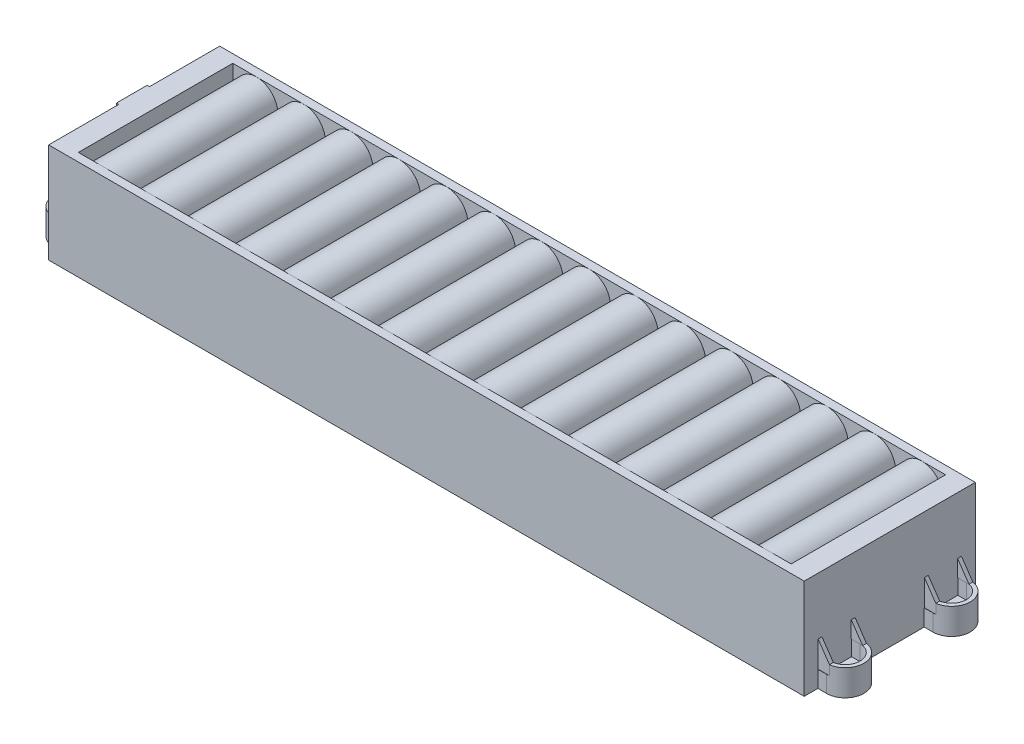
SolidWorks part; units mm, degrees
ref_plane "Front Plane" through (0, 0, 0) normal (0, 0, 1) x (1, 0, 0)
ref_plane "Top Plane" through (0, 0, 0) normal (0, 1, 0) x (1, 0, 0)
ref_plane "Right Plane" through (0, 0, 0) normal (1, 0, 0) x (0, 0, -1)
sketch "Sketch1" plane through (0, 0, 0) normal (0, 1, 0) x (1, 0, 0)
  line L1 (159, -36) -> (-159, -36)
  line L2 (159, -36) -> (159, 36)
  line L3 (159, 36) -> (-159, 36)
  line L4 (-159, -36) -> (-159, 36)
  line L5 (159, -36) -> (-159, 36) construction
  line L6 (159, 36) -> (-159, -36) construction
  point P0 (0, 0)
  dimension "D1" = 318
  dimension "D2" = 72
extrude "Boss-Extrude1" add sketch "Sketch1" along normal blind 42
sketch "Sketch2" plane through (0, 0, 0) normal (0, -1, 0) x (1, 0, 0)
  line L0 (162.625, 14.5) -> (159, 14.5)
  line L1 (159, 36) -> (159, -36) construction
  line L2 (162.625, 30.25) -> (159, 30.25)
  line L4 (162.625, 16.1) -> (159, 16.1)
  line L5 (162.625, 28.65) -> (159, 28.65)
  line L7 (159, 30.25) -> (159, 28.65)
  line L8 (159, 16.1) -> (159, 14.5)
  line L9 (162.625, -14.5) -> (159, -14.5)
  line L10 (159, -14.5) -> (159, -16.1)
  line L11 (159, -30.25) -> (162.625, -30.25)
  line L12 (159, -28.65) -> (162.625, -28.65)
  line L13 (162.625, -16.1) -> (159, -16.1)
  line L14 (159, -28.65) -> (159, -30.25)
  line L15 (-162.625, -14.5) -> (-159, -14.5)
  line L16 (-159, -36) -> (-159, 36) construction
  line L17 (-159, -14.5) -> (-159, -16.1)
  line L18 (-159, -30.25) -> (-162.625, -30.25)
  line L19 (-162.625, 14.5) -> (-159, 14.5)
  line L20 (-159, 14.5) -> (-159, 16.1)
  line L21 (-159, 30.25) -> (-162.625, 30.25)
  line L22 (-159, 28.65) -> (-162.625, 28.65)
  line L23 (-162.625, 16.1) -> (-159, 16.1)
  line L24 (-159, -28.65) -> (-162.625, -28.65)
  line L25 (-162.625, -16.1) -> (-159, -16.1)
  line L26 (-159, -28.65) -> (-159, -30.25)
  line L27 (-159, 28.65) -> (-159, 30.25)
  arc A0 (162.625, 14.5) -> (162.625, 30.25) centre (162.625, 22.375) ccw
  arc A1 (162.625, 16.1) -> (162.625, 28.65) centre (162.625, 22.375) ccw
  arc A2 (162.625, -30.25) -> (162.625, -14.5) centre (162.625, -22.375) ccw
  arc A3 (162.625, -28.65) -> (162.625, -16.1) centre (162.625, -22.375) ccw
  arc A4 (-162.625, 30.25) -> (-162.625, 14.5) centre (-162.625, 22.375) ccw
  arc A5 (-162.625, -14.5) -> (-162.625, -30.25) centre (-162.625, -22.375) ccw
  arc A6 (-162.625, 28.65) -> (-162.625, 16.1) centre (-162.625, 22.375) ccw
  arc A7 (-162.625, -16.1) -> (-162.625, -28.65) centre (-162.625, -22.375) ccw
  point P8 (159, 0)
  point P9 (170.5, 22.375)
  point P15 (170.5, -22.375)
  point P26 (-170.5, 22.375)
  point P28 (-170.5, -22.375)
  point P40 (-159, 0)
  dimension "D1" = 14.5
  dimension "D2" = 15.75
  dimension "D3" = 11.5
  dimension "D5" = 14.5
  dimension "D6" = 15.75
  dimension "D7" = 11.5
  dimension "D9" = 14.5
  dimension "D10" = 14.5
  dimension "D11" = 15.75
  dimension "D12" = 15.75
  dimension "D13" = 11.5
  dimension "D14" = 11.5
  dimension "D4" = 1.6
  dimension "D8" = 1.6
  dimension "D15" = 1.6
  dimension "D16" = 1.6
extrude "Boss-Extrude2" add sketch "Sketch2" against normal blind 11 separate body
sketch "Sketch3" plane through (0, 0, 0) normal (0, -1, 0) x (1, 0, 0)
  line L0 (159, 28.65) -> (159, 16.1)
  line L1 (159, 16.1) -> (162.625, 16.1)
  line L2 (162.625, 28.65) -> (159, 28.65)
  line L3 (161.825, 22.375) -> (165.075, 22.375) construction
  line L4 (161.825, 24.55) -> (165.075, 24.55)
  line L5 (161.825, 20.2) -> (165.075, 20.2)
  arc A0 (162.625, 28.65) -> (162.625, 16.1) centre (162.625, 22.375) cw
  arc A1 (161.825, 24.55) -> (161.825, 20.2) centre (161.825, 22.375) ccw
  arc A2 (165.075, 20.2) -> (165.075, 24.55) centre (165.075, 22.375) ccw
  arc A3 (162.625, 14.5) -> (162.625, 30.25) centre (162.625, 22.375) ccw construction
  point P13 (163.45, 22.375)
  point P18 (167.25, 22.375)
  point P19 (170.5, 22.375)
  dimension "D1" = 2.175
  dimension "D2" = 3.25
  dimension "D3" = 3.25
extrude "Boss-Extrude3" add sketch "Sketch3" against normal blind 4.5
mirror "Mirror5" about plane through (0, 0, 0) normal (1, 0, 0) of "Boss-Extrude3" second plane through (0, 0, 0) second plane normal (0, 0, 1)
sketch "Sketch4" plane through (0, 0, 0) normal (0, 0, 1) x (1, 0, 0)
  line L2 (-159, 42) -> (159, 42) construction
  line L3 (-159, 42) -> (-159, 0) construction
  line L10 (-131, 33) -> (-130, 33)
  line L11 (-130, 33) -> (-130, 42)
  line L12 (-159, 42) -> (159, 42) construction
  line L13 (-130, 42) -> (-150, 42)
  line L14 (-150, 42) -> (-150, 33)
  line L15 (-150, 33) -> (-149, 33)
  arc A0 (-131, 33) -> (-149, 33) centre (-140, 33) ccw
  point P2 (-140, 42)
  dimension "D1" = 18
  dimension "D2" = 19
  dimension "D3" = 1
  dimension "D4" = 1
extrude "Cut-Extrude1" cut sketch "Sketch4" against normal blind 32.5 and the other way blind 32.5
pattern_linear "LPattern1" count 15 spacing 20 along (1, 0, 0) of "Cut-Extrude1"
ref_plane "Plane1" through (0, 21, 0) normal (0, -1, 0) x (-1, 0, 0)
mirror "Mirror7" about plane through (0, 21, 0) normal (0, -1, 0) of "LPattern1", "Cut-Extrude1"
sketch "Sketch5" plane through (0, 0, 36) normal (0, 0, 1) x (1, 0, 0)
  line L0 (159, 11) -> (163.8, 11)
  line L1 (170.5, 11) -> (162.625, 11) construction
  line L2 (163.8, 11) -> (159, 18)
  line L3 (159, 42) -> (159, 0) construction
  line L4 (159, 18) -> (159, 11)
  dimension "D1" = 7
  dimension "D2" = 4.8
extrude "Boss-Extrude4" add sketch "Sketch5" against normal through all
sketch "Sketch6" plane through (0, 42, 0) normal (0, 1, 0) x (1, 0, 0)
  line L0 (159, -36) -> (159, 36) construction
  line L1 (159, -36) -> (163.8, -36)
  line L2 (159, -36) -> (159, -30.1618)
  line L3 (159, -30.1618) -> (163.8, -30.1618)
  line L4 (163.8, -36) -> (163.8, -30.1618)
  line L5 (163.8, -28.539) -> (159, -28.539)
  line L6 (163.8, -28.539) -> (163.8, -16.211)
  line L7 (163.8, -16.211) -> (159, -16.211)
  line L8 (159, -28.539) -> (159, -16.211)
  line L9 (163.8, -16.211) -> (163.8, -28.539) construction
  line L10 (159, 36) -> (159, -36) construction
  line L11 (163.8, -14.5882) -> (159, -14.5882)
  line L12 (163.8, -14.5882) -> (163.8, 14.5882)
  line L13 (163.8, 14.5882) -> (159, 14.5882)
  line L14 (159, -14.5882) -> (159, 14.5882)
  line L15 (163.8, 14.5882) -> (163.8, -14.5882) construction
  line L16 (163.8, 28.539) -> (163.8, 16.211) construction
  line L17 (163.8, 16.211) -> (159, 16.211)
  line L18 (163.8, 16.211) -> (163.8, 28.539)
  line L19 (163.8, 28.539) -> (159, 28.539)
  line L20 (159, 16.211) -> (159, 28.539)
  line L22 (159, 36) -> (163.8, 36)
  line L23 (159, 36) -> (159, 30.1618)
  line L24 (159, 30.1618) -> (163.8, 30.1618)
  line L25 (163.8, 36) -> (163.8, 30.1618)
  arc A0 (162.625, -28.65) -> (162.625, -16.1) centre (162.625, -22.375) ccw construction
  arc A1 (163.8, 14.5882) -> (163.8, 30.1618) centre (162.625, 22.375) ccw construction
  arc A2 (162.625, 16.1) -> (162.625, 28.65) centre (162.625, 22.375) ccw construction
extrude "Cut-Extrude2" cut sketch "Sketch6" against normal blind 35
sketch "Sketch7" plane through (-159, 0, 0) normal (-1, 0, 0) x (0, 0, 1)
  line L0 (-36, 42) -> (36, 42) construction
  line L1 (-6.5, 42) -> (6.5, 42)
  line L2 (-6.5, 42) -> (-6.5, 32)
  line L3 (-6.5, 32) -> (6.5, 32)
  line L4 (6.5, 42) -> (6.5, 32)
  point P6 (0, 42)
  point P7 (0, 42)
  dimension "D1" = 13
  dimension "D2" = 10
extrude "Boss-Extrude5" add sketch "Sketch7" along normal blind 1
sketch "Sketch8" plane through (0, 4.5, 0) normal (0, 1, 0) x (1, 0, 0)
  line L1 (-168.9, -22.375) -> (-159, -22.375) construction
  line L2 (-159, -28.65) -> (-159, -16.1) construction
  line L3 (-159, -6.5) -> (-159, -36) construction
  line L4 (-162.625, -28.65) -> (-159, -28.65) construction
  line L5 (-159, -16.1) -> (-162.625, -16.1) construction
  line L6 (-162.625, -28.65) -> (-159, -28.65)
  line L7 (-159, -16.1) -> (-162.625, -16.1)
  line L8 (-159, -28.65) -> (-159, -16.1)
  arc A1 (-162.625, -16.1) -> (-162.625, -28.65) centre (-162.625, -22.375) ccw construction
  circle A2 centre (-164, -22.375) radius 4.75
  arc A3 (-162.625, -16.1) -> (-162.625, -28.65) centre (-162.625, -22.375) ccw
  dimension "D1" = 5
  dimension "D2" = 9.5
extrude "Boss-Extrude6" add sketch "Sketch8" along normal up to surface (6.5 mm away) up to face at (-162.5813, 11, 22.375)
mirror "Mirror8" about plane through (0, 0, 0) normal (0, 0, 1) of "Boss-Extrude6"
sketch "Sketch9" plane through (0, 4.5, 0) normal (0, 1, 0) x (1, 0, 0)
  line L0 (-159.65, 22.375) -> (-167.25, 22.375) construction
  line L1 (167.25, 22.375) -> (159.65, 22.375) construction
  line L2 (167.25, -22.375) -> (159, -22.375)
  line L3 (159, -28.65) -> (159, -16.1) construction
  arc A0 (-161.825, 20.2) -> (-161.825, 24.55) centre (-161.825, 22.375) ccw construction
  arc A1 (-165.075, 24.55) -> (-165.075, 20.2) centre (-165.075, 22.375) ccw construction
  arc A2 (165.075, 20.2) -> (165.075, 24.55) centre (165.075, 22.375) ccw construction
  arc A3 (161.825, 24.55) -> (161.825, 20.2) centre (161.825, 22.375) ccw construction
  arc A4 (165.075, -24.55) -> (165.075, -20.2) centre (165.075, -22.375) ccw construction
  point P16 (-163.45, 22.375)
  point P17 (163.45, 22.375)
  dimension "D1" = 326.9
  dimension "D2" = 44.75
equation "\"D1@Sketch2\"=29/2"
equation "\"D1@Sketch3\"=4.35/2"
equation "\"D2@Sketch3\"=7.6-2*\"D1@Sketch3\""
equation "\"D5@Sketch2\"=\"D1@Sketch2\""
equation "\"D6@Sketch2\"=\"D2@Sketch2\""
equation "\"D7@Sketch2\"=\"D3@Sketch2\""
equation "\"D9@Sketch2\"=\"D1@Sketch2\""
equation "\"D10@Sketch2\"=\"D1@Sketch2\""
equation "\"D11@Sketch2\"=\"D2@Sketch2\""
equation "\"D12@Sketch2\"=\"D2@Sketch2\""
equation "\"D13@Sketch2\"=\"D3@Sketch2\""
equation "\"D14@Sketch2\"=\"D3@Sketch2\""
